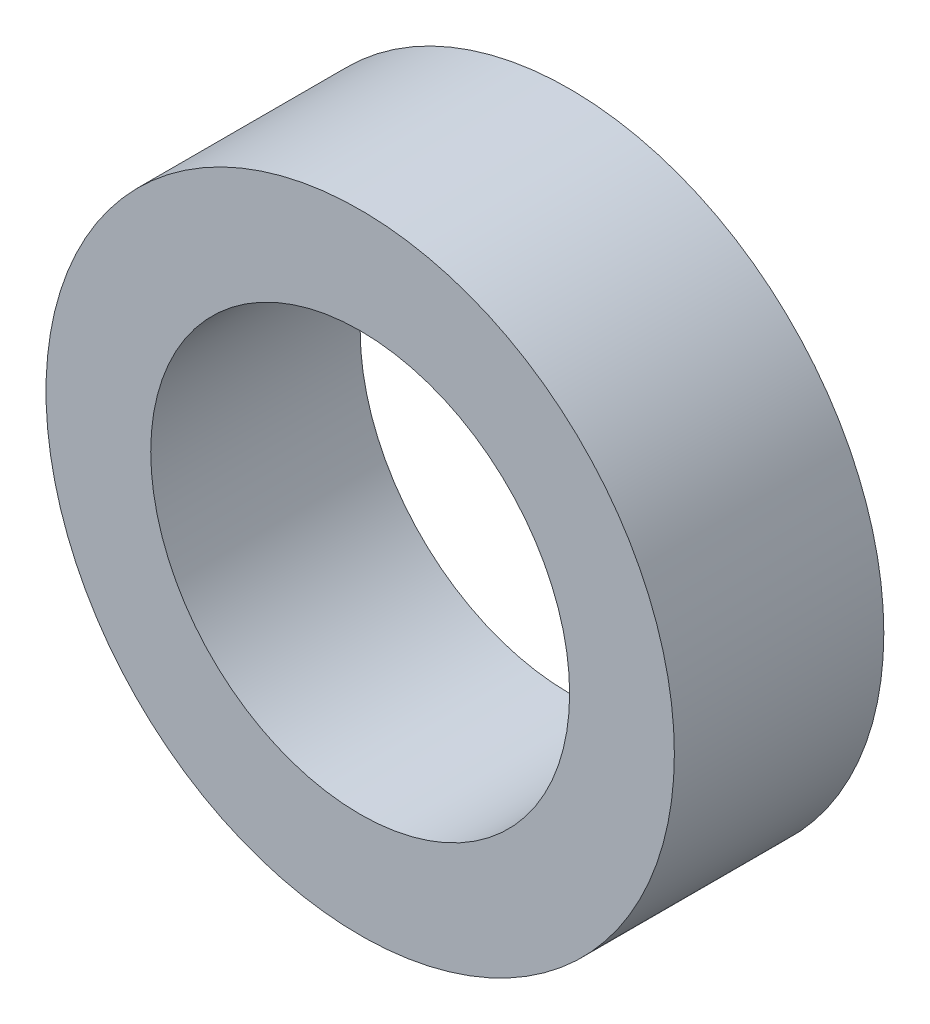
SolidWorks part; units mm, degrees
ref_plane "前视基准面" through (0, 0, 0) normal (0, 0, 1) x (1, 0, 0)
ref_plane "上视基准面" through (0, 0, 0) normal (0, 1, 0) x (1, 0, 0)
ref_plane "右视基准面" through (0, 0, 0) normal (1, 0, 0) x (0, 0, -1)
sketch "草图1" plane through (0, 0, 0) normal (0, 0, 1) x (1, 0, 0)
  circle A0 centre (0, 0) radius 7.5
  circle A1 centre (0, 0) radius 5
  dimension "D1" = 15
  dimension "D2" = 10
extrude "凸台-拉伸1" add sketch "草图1" along normal blind 5
